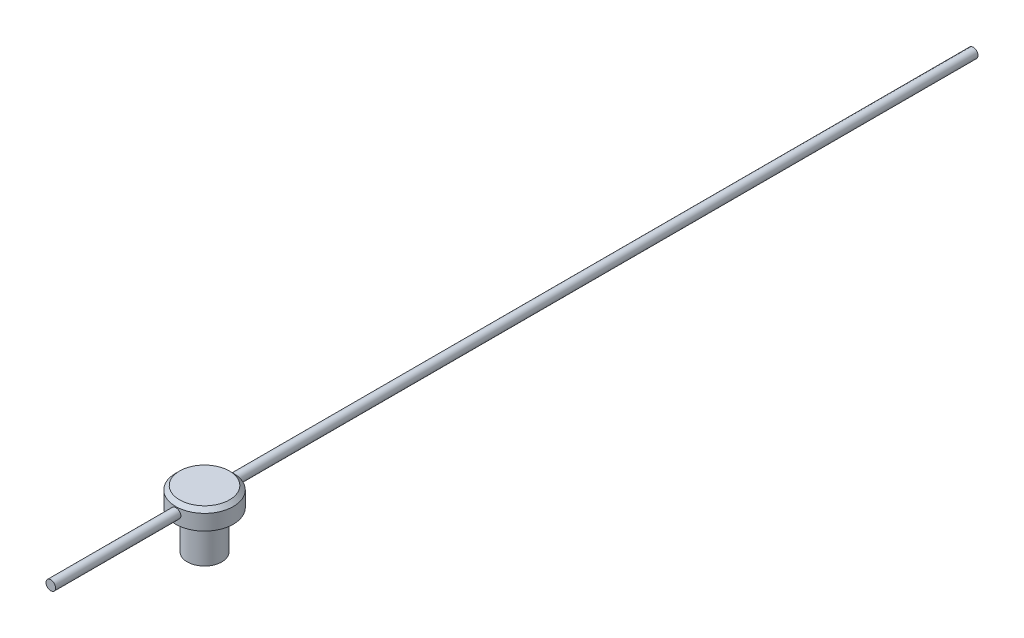
SolidWorks part; units mm, degrees
ref_plane "Front Plane" through (0, 0, 0) normal (0, 0, 1) x (1, 0, 0)
ref_plane "Top Plane" through (0, 0, 0) normal (0, 1, 0) x (1, 0, 0)
ref_plane "Right Plane" through (0, 0, 0) normal (1, 0, 0) x (0, 0, -1)
sketch "Sketch1" plane through (0, 0, 0) normal (0, 1, 0) x (1, 0, 0)
  circle A0 centre (0, 0) radius 0.45
  dimension "D1" = 0.9
extrude "Boss-Extrude1" add sketch "Sketch1" along normal blind 1
sketch "Sketch2" plane through (0, 1, 0) normal (0, 1, 0) x (1, 0, 0)
  circle A0 centre (0, 0) radius 0.75
  dimension "D1" = 1.5
extrude "Boss-Extrude2" add sketch "Sketch2" along normal blind 0.5
sketch "Sketch3" plane through (0, 0, 0) normal (0, 0, 1) x (1, 0, 0)
  circle A0 centre (0, 1.25) radius 0.125
  dimension "D1" = 0.25
extrude "Boss-Extrude3" add sketch "Sketch3" against normal blind 20 and the other way blind 4
chamfer "Chamfer1" distance 0.1 angle 45 1 edges at (0, 1.5, 0.75)
